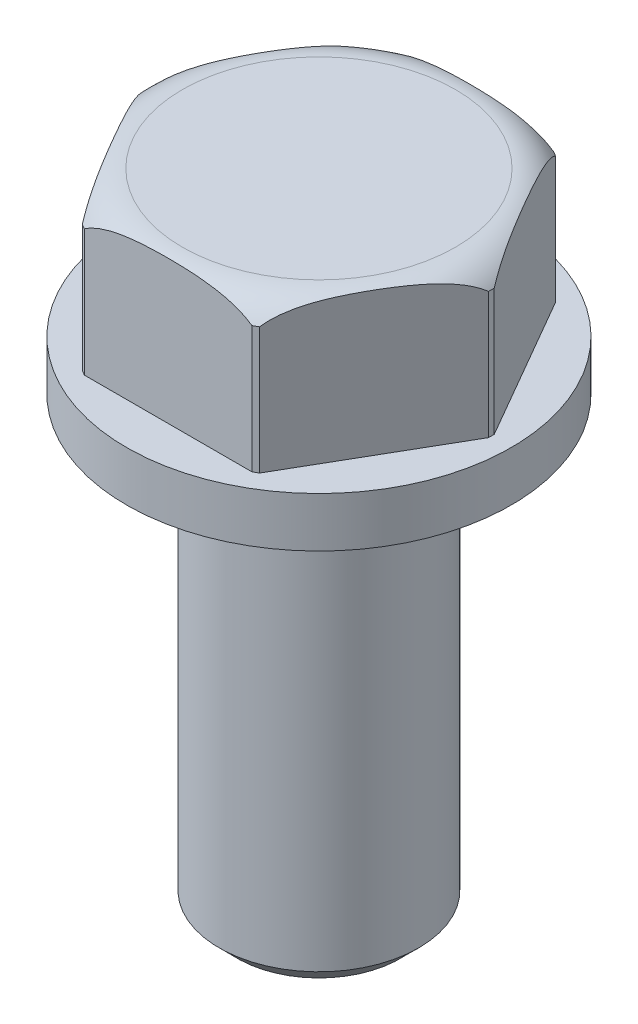
SolidWorks part; units mm, degrees
ref_plane "Front Plane" through (0, 0, 0) normal (0, 0, 1) x (1, 0, 0)
ref_plane "Top Plane" through (0, 0, 0) normal (0, 1, 0) x (1, 0, 0)
ref_plane "Right Plane" through (0, 0, 0) normal (1, 0, 0) x (0, 0, -1)
sketch "Sketch1" plane through (0, 0, 0) normal (0, 0, 1) x (1, 0, 0)
  line L0 (0, 0) -> (6.35, 0)
  line L1 (6.35, 0) -> (6.35, 28.5496)
  line L2 (6.35, 28.5496) -> (12.2555, 28.5496)
  line L3 (12.2555, 28.5496) -> (12.2555, 31.7246)
  line L4 (12.2555, 31.7246) -> (10.9855, 31.7246)
  line L5 (10.9855, 31.7246) -> (10.9855, 40.9956)
  line L6 (10.9855, 40.9956) -> (0, 40.9956)
  line L7 (0, 40.9956) -> (0, 0) construction
  line L8 (0, 0) -> (0, 40.9956)
  dimension "D1" = 12.7
  dimension "D2" = 21.971
  dimension "D3" = 24.511
  dimension "D4" = 40.9956
  dimension "D5" = 9.271
  dimension "D6" = 3.175
revolve "Revolve1" add sketch "Sketch1" angle 360 about L7
sketch "Sketch2" plane through (0, 40.9956, 0) normal (0, 1, 0) x (1, 0, 0)
  line L1 (-5.334, 13.7156) -> (5.334, 13.7156)
  line L2 (-5.334, 13.7156) -> (-5.334, 9.6036)
  line L3 (-5.334, 9.6036) -> (5.334, 9.6036)
  line L4 (5.334, 13.7156) -> (5.334, 9.6036)
  circle A0 centre (0, 0) radius 10.9855 construction
  circle A1 centre (0, 0) radius 10.9855 construction
  dimension "D1" = 10.668
extrude "Cut-Extrude1" cut sketch "Sketch2" against normal up to surface (9.271 mm away) up to face at (-10.9855, 31.7246, 0)
pattern_circular "CirPattern1" count 6 over 360 about axis through (0, 0, 0) along (0, 1, 0) of "Cut-Extrude1"
sketch "Sketch4" plane through (0, 0, 0) normal (0, 0, 1) x (1, 0, 0)
  line L0 (11.176, 39.4716) -> (11.176, 40.9956)
  line L1 (11.176, 40.9956) -> (8.6995, 40.9956)
  line L2 (10.984, 40.9956) -> (5.65, 40.9956) construction
  line L3 (0, -5.0426) -> (0, 51.1772) construction
  arc A0 (11.176, 39.4716) -> (8.6995, 40.9956) centre (8.6995, 38.2214) ccw
  dimension "D1" = 22.352
  dimension "D2" = 17.399
  dimension "D3" = 1.524
revolve "Cut-Revolve1" cut sketch "Sketch4" angle 360 about L3
chamfer "Chamfer1" distance 1.1633 angle 45 1 edges at (-6.35, 0, 0)
